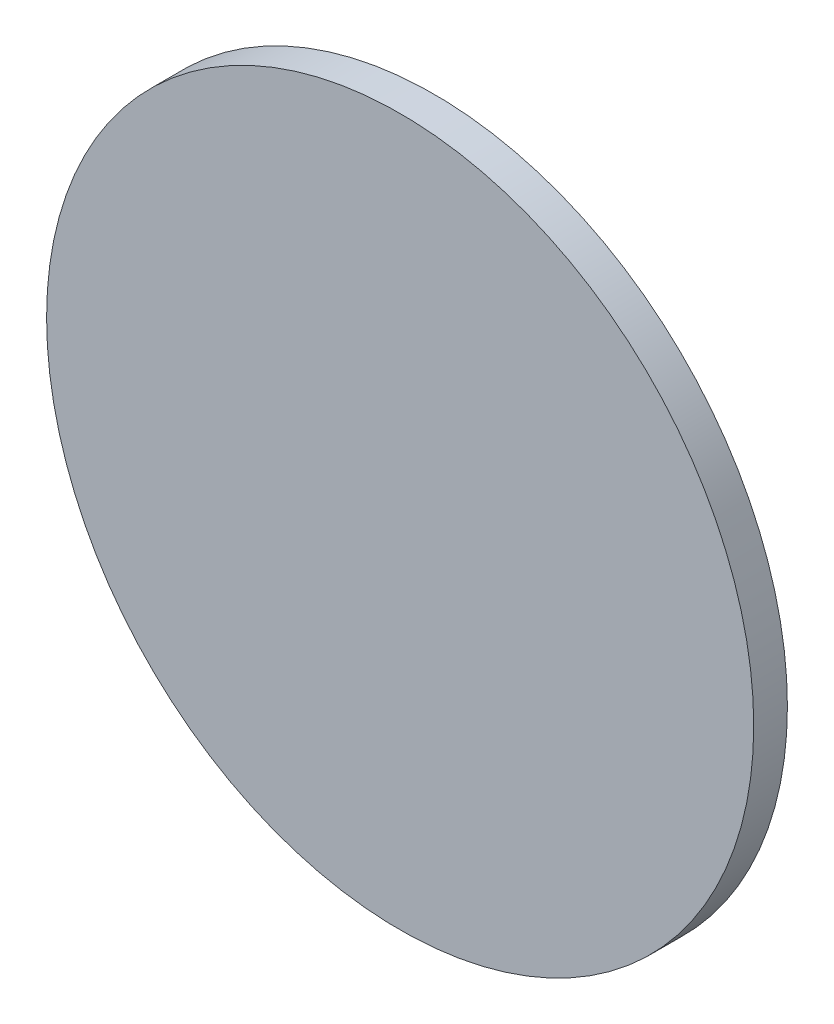
SolidWorks part; units mm, degrees
ref_plane "Front Plane" through (0, 0, 0) normal (0, 0, 1) x (1, 0, 0)
ref_plane "Top Plane" through (0, 0, 0) normal (0, 1, 0) x (1, 0, 0)
ref_plane "Right Plane" through (0, 0, 0) normal (1, 0, 0) x (0, 0, -1)
sketch "Sketch1" plane through (0, 0, 0) normal (0, 0, 1) x (1, 0, 0)
  circle A0 centre (0, 0) radius 53.34
  dimension "D1" = 106.68
extrude "Boss-Extrude1" add sketch "Sketch1" along normal blind 5.08
equation "\"D1@Boss-Extrude1\" = \"Material\""
equation "\"Material\"= .2"
equation "\"D1@Sketch1\" = \"Platform_Diameter\""
equation "\"Platform_Diameter\"= 4.2"
